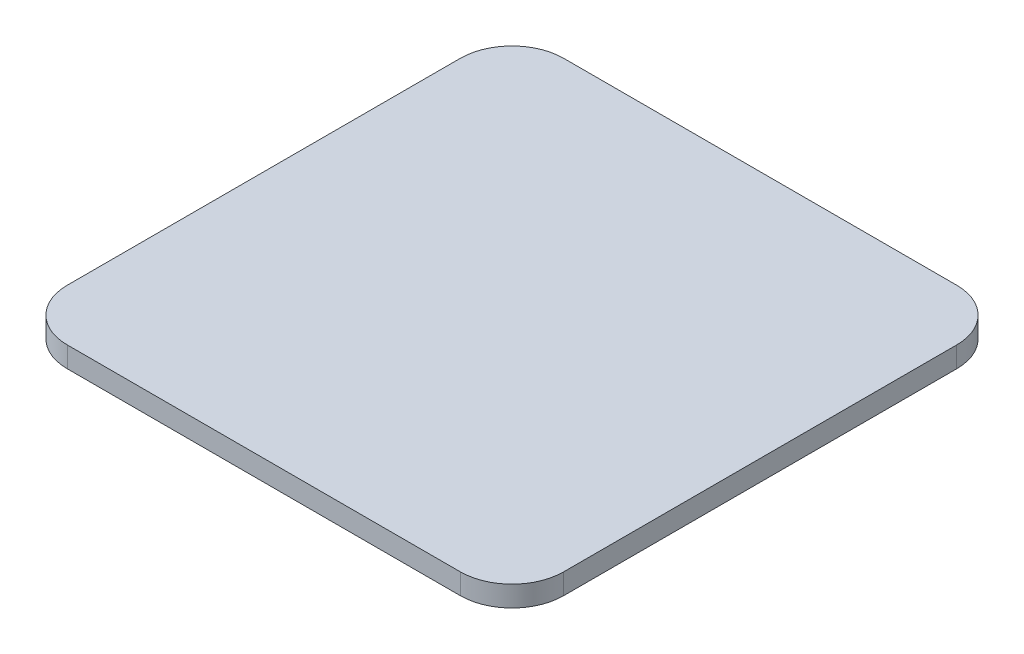
SolidWorks part; units mm, degrees
ref_plane "Front Plane" through (0, 0, 0) normal (0, 0, 1) x (1, 0, 0)
ref_plane "Top Plane" through (0, 0, 0) normal (0, 1, 0) x (1, 0, 0)
ref_plane "Right Plane" through (0, 0, 0) normal (1, 0, 0) x (0, 0, -1)
sketch "Sketch1" plane through (0, 0, 0) normal (0, 1, 0) x (1, 0, 0)
  line L1 (-19, 24) -> (19, 24)
  line L2 (-24, 19) -> (-24, -19)
  line L3 (-19, -24) -> (19, -24)
  line L4 (24, 19) -> (24, -19)
  line L5 (-24, 24) -> (24, -24) construction
  line L6 (-24, -24) -> (24, 24) construction
  arc A0 (19, -24) -> (24, -19) centre (19, -19) ccw
  arc A1 (-19, -24) -> (-24, -19) centre (-19, -19) cw
  arc A2 (-19, 24) -> (-24, 19) centre (-19, 19) ccw
  arc A3 (24, 19) -> (19, 24) centre (19, 19) ccw
  point P0 (0, 0)
  dimension "D3" = 5
  dimension "D1" = 48
  dimension "D2" = 48
extrude "Boss-Extrude1" add sketch "Sketch1" along normal blind 2
